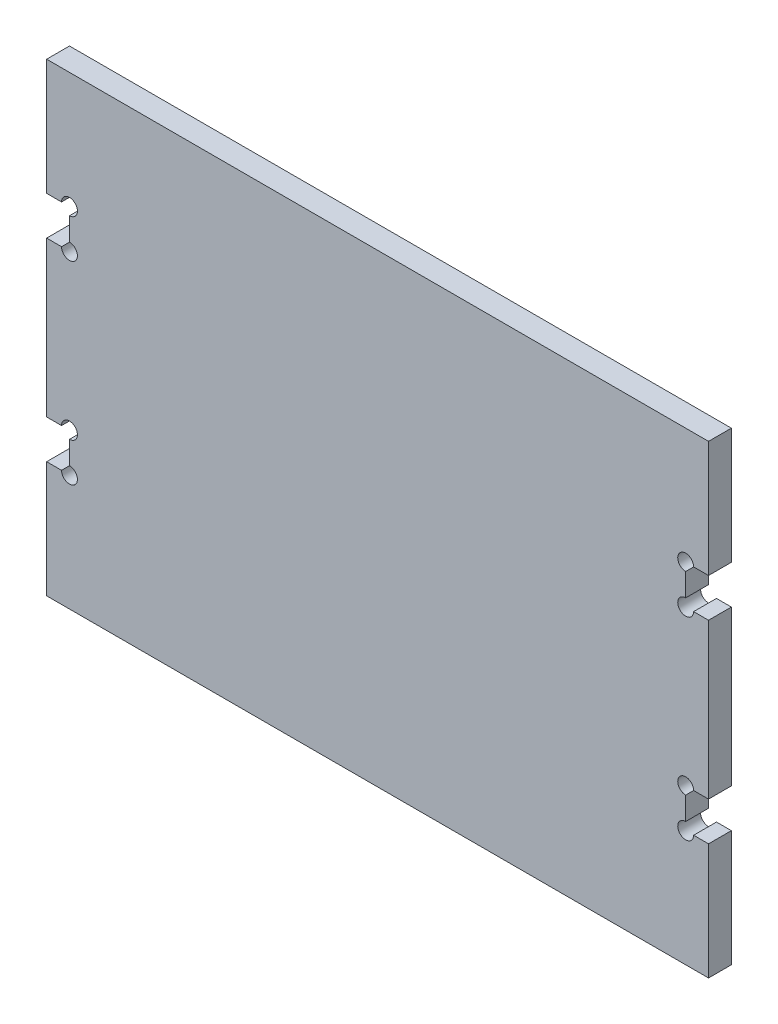
SolidWorks part; units mm, degrees
ref_plane "Front Plane" through (0, 0, 0) normal (0, 0, 1) x (1, 0, 0)
ref_plane "Top Plane" through (0, 0, 0) normal (0, 1, 0) x (1, 0, 0)
ref_plane "Right Plane" through (0, 0, 0) normal (1, 0, 0) x (0, 0, -1)
sketch "Sketch1" plane through (0, 0, 0) normal (0, 0, 1) x (1, 0, 0)
  line L1 (85.45, -60) -> (-85.45, -60)
  line L2 (85.45, -60) -> (85.45, 60)
  line L3 (85.45, 60) -> (-85.45, 60)
  line L4 (-85.45, -60) -> (-85.45, 60)
  line L5 (85.45, -60) -> (-85.45, 60) construction
  line L6 (85.45, 60) -> (-85.45, -60) construction
  point P0 (0, 0)
  dimension "D1" = 170.9
  dimension "D2" = 120
extrude "Boss-Extrude1" add sketch "Sketch1" along normal blind 5.9
sketch "Sketch2" plane through (0, 0, 5.9) normal (0, 0, 1) x (1, 0, 0)
  line L0 (85.45, -60) -> (85.45, 60) construction
  line L1 (85.45, 30) -> (79.55, 30)
  line L2 (85.45, 30) -> (85.45, 20)
  line L3 (85.45, 20) -> (79.55, 20)
  line L4 (79.55, 30) -> (79.55, 20)
  line L5 (85.45, 60) -> (-85.45, 60) construction
  line L6 (0, 0) -> (0, 30.9081) construction
  line L7 (85.45, -20) -> (79.55, -20)
  line L8 (85.45, -20) -> (85.45, -30)
  line L9 (85.45, -30) -> (79.55, -30)
  line L10 (79.55, -20) -> (79.55, -30)
  line L11 (-79.55, -20) -> (-79.55, -30)
  line L12 (-85.45, -30) -> (-79.55, -30)
  line L13 (-85.45, -20) -> (-85.45, -30)
  line L14 (-85.45, -20) -> (-79.55, -20)
  line L15 (-79.55, 30) -> (-79.55, 20)
  line L16 (-85.45, 20) -> (-79.55, 20)
  line L17 (-85.45, 30) -> (-85.45, 20)
  line L18 (-85.45, 30) -> (-79.55, 30)
  dimension "D1" = 5.9
  dimension "D2" = 10
  dimension "D3" = 30
  dimension "D4" = 40
extrude "Cut-Extrude1" cut sketch "Sketch2" against normal through all
sketch "Sketch3" plane through (0, 0, 5.9) normal (0, 0, 1) x (1, 0, 0)
  line L0 (-20.25, 0) -> (0, 0) construction
  line L1 (0, 0) -> (20.25, 0) construction
  circle A0 centre (0, 0) radius 50 construction
  circle A2 centre (-20.25, 0) radius 2.05
  circle A3 centre (20.25, 0) radius 2.05
  dimension "D1" = 100
  dimension "D2" = 4.1
  dimension "D3" = 40.5
sketch "Sketch4" plane through (0, 0, 5.9) normal (0, 0, 1) x (1, 0, 0)
  line L0 (0, 0) -> (0, 60) construction
  line L2 (85.45, 60) -> (-85.45, 60) construction
  line L4 (-15, 18.4) -> (15, 18.4)
  line L5 (-15, 18.4) -> (-15, 22.5)
  line L6 (-15, 22.5) -> (15, 22.5)
  line L7 (15, 18.4) -> (15, 22.5)
  line L8 (-15, 18.4) -> (15, 22.5) construction
  line L9 (-15, 22.5) -> (15, 18.4) construction
  point P5 (0, 20.45)
  dimension "D1" = 4.1
  dimension "D2" = 30
  dimension "D3" = 37.5
sketch "Sketch5" plane through (0, 0, 5.9) normal (0, 0, 1) x (1, 0, 0)
  circle A0 centre (-79.55, 30) radius 2.05
  circle A1 centre (-79.55, 20) radius 2.05
  circle A2 centre (-79.55, -20) radius 2.05
  circle A3 centre (-79.55, -30) radius 2.05
  circle A4 centre (79.55, -20) radius 2.05
  circle A5 centre (79.55, -30) radius 2.05
  circle A6 centre (79.55, 20) radius 2.05
  circle A7 centre (79.55, 30) radius 2.05
  dimension "D1" = 4.1
extrude "Cut-Extrude4" cut sketch "Sketch5" against normal up to next
equation "\"e\" = 5.9"
equation "\"D1@Boss-Extrude1\"= \"e\""
equation "\"D1@Sketch2\"= \"e\""
equation "\"D1@Sketch1\" = 165 + \"e\""
